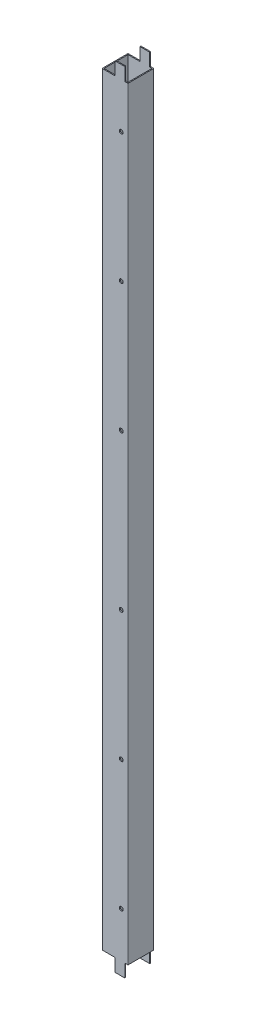
SolidWorks part; units mm, degrees
ref_plane "Front Plane" through (0, 0, 0) normal (0, 0, 1) x (1, 0, 0)
ref_plane "Top Plane" through (0, 0, 0) normal (0, 1, 0) x (1, 0, 0)
ref_plane "Right Plane" through (0, 0, 0) normal (1, 0, 0) x (0, 0, -1)
sketch "Sketch1" plane through (0, 0, 0) normal (0, 1, 0) x (1, 0, 0)
  line L0 (1.5, 1.5) -> (38.5, 1.5)
  line L1 (0.5, 0) -> (39.5, 0)
  line L2 (0, 0.5) -> (0, 39.5)
  line L3 (0.5, 40) -> (39.5, 40)
  line L4 (40, 0.5) -> (40, 39.5)
  line L5 (38.5, 1.5) -> (38.5, 38.5)
  line L6 (1.5, 38.5) -> (38.5, 38.5)
  line L7 (1.5, 1.5) -> (1.5, 38.5)
  arc A0 (39.5, 0) -> (40, 0.5) centre (39.5, 0.5) ccw
  arc A1 (0.5, 0) -> (0, 0.5) centre (0.5, 0.5) cw
  arc A2 (0, 39.5) -> (0.5, 40) centre (0.5, 39.5) cw
  arc A3 (39.5, 40) -> (40, 39.5) centre (39.5, 39.5) cw
  arc A4 (38.5, 1.5) -> (38.5, 1.5) centre (38.5, 1.5) ccw
  arc A5 (38.5, 38.5) -> (38.5, 38.5) centre (38.5, 38.5) cw
  arc A6 (1.5, 38.5) -> (1.5, 38.5) centre (1.5, 38.5) cw
  arc A7 (1.5, 1.5) -> (1.5, 1.5) centre (1.5, 1.5) cw
  point P9 (0, 0)
  dimension "D3" = 0.5
  dimension "D1" = 40
  dimension "D2" = 40
  dimension "D4" = 1.5
extrude "Boss-Extrude1" add sketch "Sketch1" along normal blind 1220
sketch "Sketch2" plane through (0, 0, 0) normal (0, 0, 1) x (1, 0, 0)
  line L10 (20, 1220) -> (20, 1200)
  line L17 (40, 1220) -> (35, 1220)
  line L18 (40, 1220) -> (40, 1200)
  line L19 (40, 1200) -> (35, 1200)
  line L20 (35, 1220) -> (35, 1200)
  line L21 (0.5, 1220) -> (39.5, 1220) construction
  line L26 (0, 610) -> (39.5, 610) construction
  line L27 (0, 1220) -> (0, 0) construction
  line L28 (39.5, 1220) -> (39.5, 0) construction
  line L37 (0, 20) -> (20, 20)
  line L38 (0, 1220) -> (20, 1220)
  line L39 (0, 1220) -> (0, 1200)
  line L40 (0, 1200) -> (20, 1200)
  line L42 (0, 0) -> (0, 20)
  line L43 (0, 0) -> (20, 0)
  line L44 (35, 0) -> (35, 20)
  line L45 (40, 20) -> (35, 20)
  line L46 (40, 0) -> (40, 20)
  line L47 (40, 0) -> (35, 0)
  line L48 (20, 0) -> (20, 20)
  dimension "D1" = 20
  dimension "D2" = 5
  dimension "D3" = 20
extrude "Cut-Extrude1" cut sketch "Sketch2" against normal blind 50
sketch "Sketch3" plane through (0, 0, 0) normal (0, 0, 1) x (1, 0, 0)
  line L0 (39.5, 20) -> (35, 20) construction
  line L1 (40, 1200) -> (40, 20) construction
  line L2 (40, 610) -> (0.5, 610) construction
  line L3 (0.5, 1200) -> (0.5, 20) construction
  circle A0 centre (29.5, 90) radius 3
  circle A1 centre (29.5, 290) radius 3
  circle A2 centre (29.5, 490) radius 3
  circle A3 centre (29.5, 730) radius 3
  circle A4 centre (29.5, 930) radius 3
  circle A5 centre (29.5, 1130) radius 3
  dimension "D1" = 70
  dimension "D2" = 6
  dimension "D3" = 10.5
  dimension "D4" = 3
extrude "Cut-Extrude2" cut sketch "Sketch3" against normal blind 10
